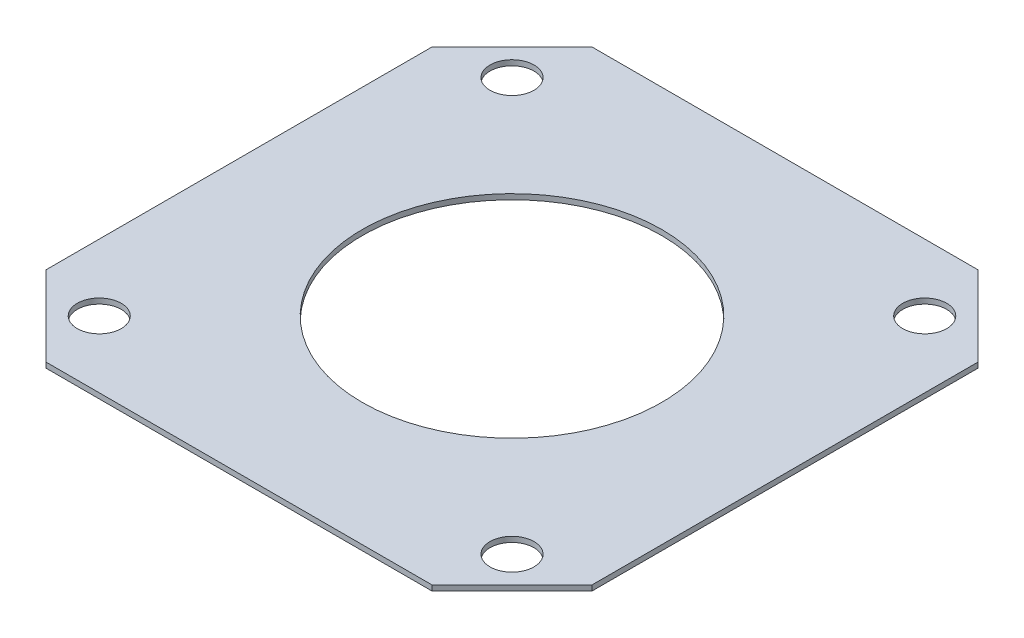
SolidWorks part; units mm, degrees
ref_plane "Front Plane" through (0, 0, 0) normal (1, 0, 0) x (0, 1, 0)
ref_plane "Top Plane" through (0, 0, 0) normal (0, 0, 1) x (0, 1, 0)
ref_plane "Right Plane" through (0, 0, 0) normal (0, 1, 0) x (-1, 0, 0)
sketch "Sketch1" plane through (0, 0, 0) normal (0, 1, 0) x (-1, 0, 0)
  line L1 (-20.5, 20.5) -> (20.5, 20.5)
  line L2 (-20.5, 20.5) -> (-20.5, -20.5)
  line L3 (-20.5, -20.5) -> (20.5, -20.5)
  line L4 (20.5, 20.5) -> (20.5, -20.5)
  line L5 (-20.5, 20.5) -> (20.5, -20.5) construction
  line L6 (-20.5, -20.5) -> (20.5, 20.5) construction
  circle A0 centre (0, 0) radius 11.25
  circle A1 centre (15.5, 15.5) radius 1.65
  circle A2 centre (-15.5, 15.5) radius 1.65
  circle A3 centre (-15.5, -15.5) radius 1.65
  circle A4 centre (15.5, -15.5) radius 1.65
  point P9 (20.5, 0)
  point P10 (-15.497, 15.497)
  point P11 (15.5, -15.5)
  point P18 (-15.5, -15.5)
  dimension "D1" = 22.5
  dimension "D5" = 3.3
  dimension "D2" = 41
  dimension "D3" = 41
  dimension "D4" = 15.5
  dimension "D6" = 2
  dimension "D7" = 2
extrude "Boss-Extrude1" add sketch "Sketch1" along normal blind 0.4
chamfer "Chamfer1" distance 6 angle 45 4 edges at (20.5, 0.2, 20.5) (20.5, 0.2, -20.5) (-20.5, 0.2, 20.5) (-20.5, 0.2, -20.5)
